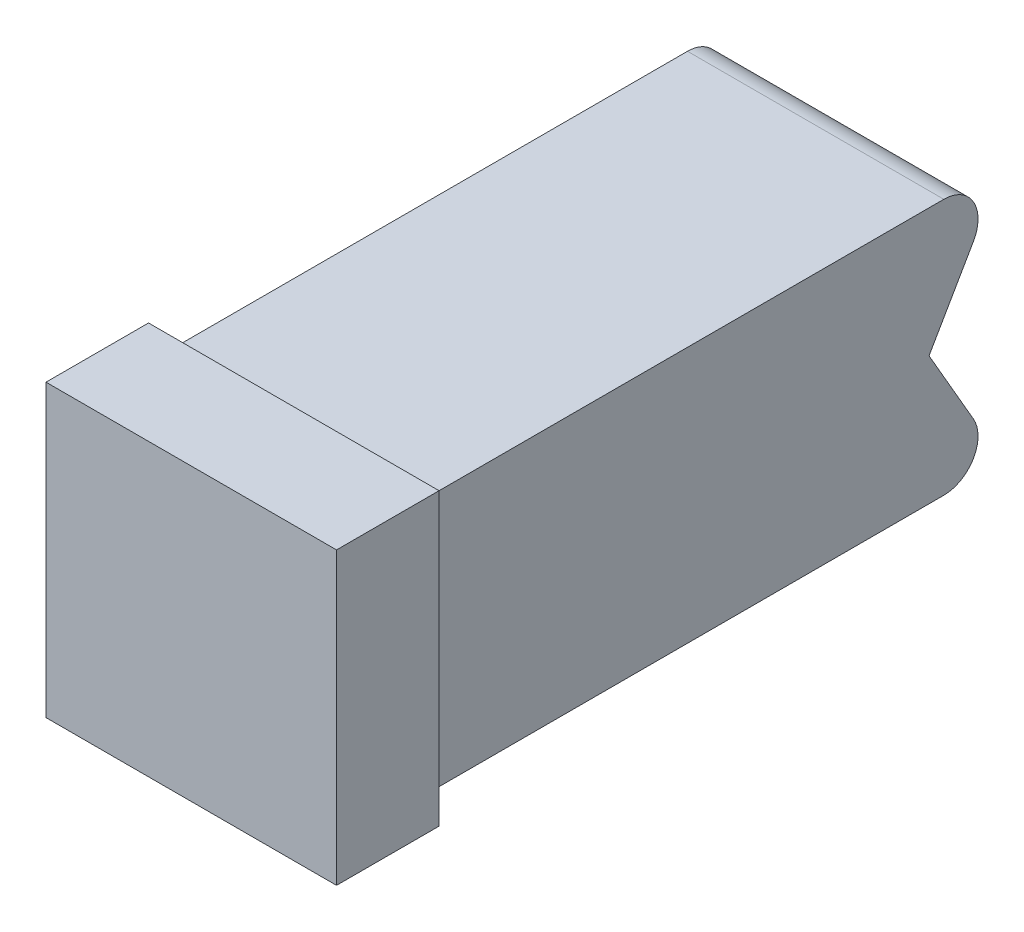
SolidWorks part; units mm, degrees
ref_plane "Front Plane" through (0, 0, 0) normal (0, 0, 1) x (1, 0, 0)
ref_plane "Top Plane" through (0, 0, 0) normal (0, 1, 0) x (1, 0, 0)
ref_plane "Right Plane" through (0, 0, 0) normal (1, 0, 0) x (0, 0, -1)
ref_plane "Plane1" through (0.5, 0, 0) normal (-1, 0, 0) x (0, -1, 0)
sketch "Sketch1" plane through (0.5, 0, 0) normal (-1, 0, 0) x (0, -1, 0)
  line L0 (-0.5, 3) -> (-8, 3)
  line L1 (-8, 3) -> (-8, -15.2679)
  line L2 (-6.5, -16.134) -> (-4.25, -14.8349)
  line L3 (-4.25, -14.8349) -> (-2, -16.134)
  line L4 (-0.5, -15.2679) -> (-0.5, 3)
  arc A0 (-8, -15.2679) -> (-6.5, -16.134) centre (-7, -15.2679) ccw
  arc A1 (-2, -16.134) -> (-0.5, -15.2679) centre (-1.5, -15.2679) ccw
extrude "Boss-Extrude1" add sketch "Sketch1" against normal blind 7.5
sketch "Sketch2" plane through (0, 8, 0) normal (0, 1, 0) x (-1, 0, 0)
  line L0 (-8, 3) -> (-0.5, 3)
  line L1 (-0.5, 3) -> (-0.5, -15.2679)
  line L2 (-0.5, -15.2679) -> (-8, -15.2679)
  line L3 (-8, -15.2679) -> (-8, 3)
extrude "Boss-Extrude2" add sketch "Sketch2" along normal blind 0.5
sketch "Sketch3" plane through (8, 0, 0) normal (1, 0, 0) x (0, 0, -1)
  line L0 (-3, 0.5) -> (-3, 8.5)
  line L1 (-3, 8.5) -> (15.2679, 8.5)
  line L2 (15.2679, 8.5) -> (15.2679, 0.5)
  line L3 (15.2679, 0.5) -> (-3, 0.5)
extrude "Boss-Extrude3" add sketch "Sketch3" along normal blind 0.5
sketch "Sketch4" plane through (0, 0.5, 0) normal (0, -1, 0) x (1, 0, 0)
  line L0 (0.5, 3) -> (8.5, 3)
  line L1 (8.5, 3) -> (8.5, -15.2679)
  line L2 (8.5, -15.2679) -> (0.5, -15.2679)
  line L3 (0.5, -15.2679) -> (0.5, 3)
extrude "Boss-Extrude4" add sketch "Sketch4" along normal blind 0.5
sketch "Sketch5" plane through (0, 0, -15.2679) normal (0, 0, -1) x (-1, 0, 0)
  line L0 (-0.5, 8) -> (-0.5, 8.5)
  line L1 (-0.5, 8.5) -> (-8.5, 8.5)
  line L2 (-8.5, 8.5) -> (-8.5, 0)
  line L3 (-8.5, 0) -> (-0.5, 0)
  line L4 (-0.5, 0) -> (-0.5, 0.5)
  line L5 (-0.5, 0.5) -> (-8, 0.5)
  line L6 (-8, 0.5) -> (-8, 4.25)
  line L7 (-8, 4.25) -> (-8, 8)
  line L8 (-8, 8) -> (-0.5, 8)
extrude "Cut-Extrude1" cut sketch "Sketch5" against normal blind 0.433
sketch "Sketch6" plane through (0, 0, -14.8349) normal (0, 0, -1) x (-1, 0, 0)
  line L0 (-0.5, 8) -> (-0.5, 8.5)
  line L1 (-0.5, 8.5) -> (-8.5, 8.5)
  line L2 (-8.5, 8.5) -> (-8.5, 0)
  line L3 (-8.5, 0) -> (-0.5, 0)
  line L4 (-0.5, 0) -> (-0.5, 0.5)
  line L5 (-0.5, 0.5) -> (-8, 0.5)
  line L6 (-8, 0.5) -> (-8, 8)
  line L7 (-8, 8) -> (-0.5, 8)
extrude "Cut-Extrude2" cut sketch "Sketch6" against normal blind 14.8349
sketch "Sketch7" plane through (0.5, 0, 0) normal (-1, 0, 0) x (0, 0, 1)
  line L0 (3, 8.5) -> (3, 0)
  line L1 (3, 0) -> (0, 0)
  line L2 (0, 0) -> (0, 8.5)
  line L3 (0, 8.5) -> (3, 8.5)
extrude "Boss-Extrude5" add sketch "Sketch7" along normal blind 0.5
